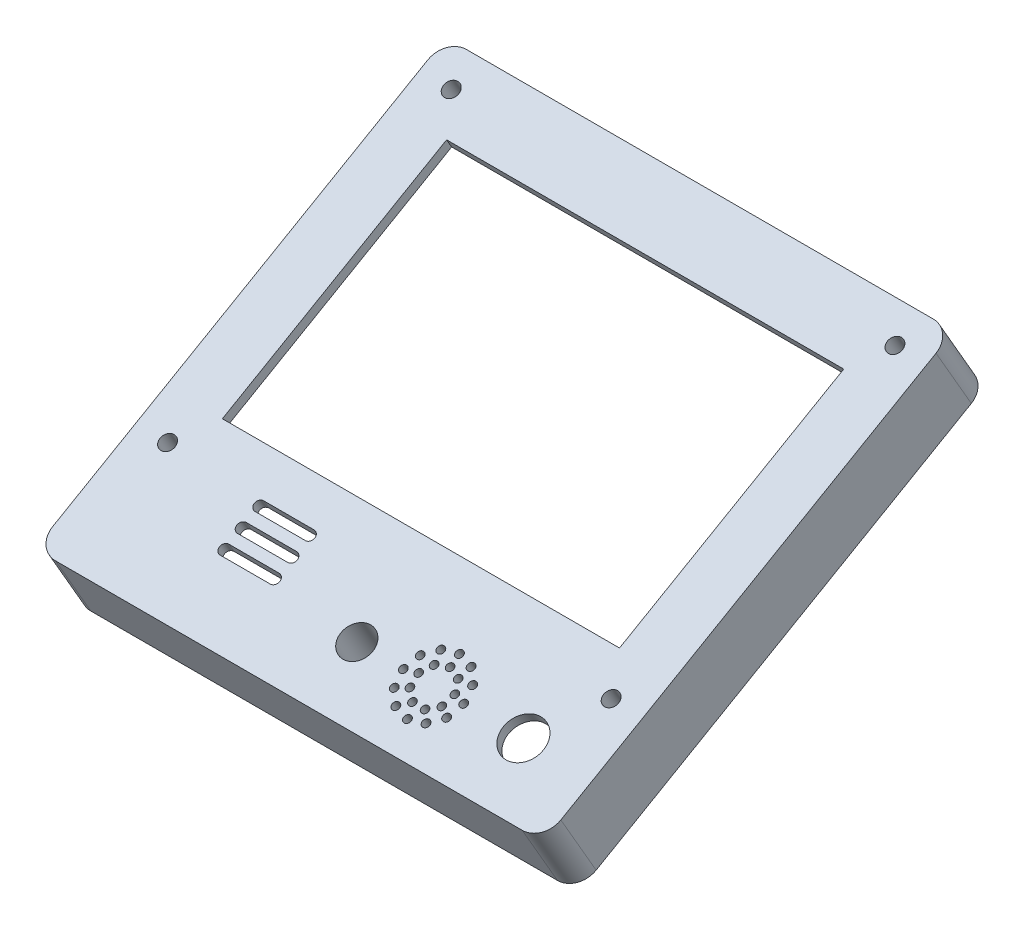
SolidWorks part; units mm, degrees
ref_plane "Front Plane" through (0, 0, 0) normal (0, 0, 1) x (1, 0, 0)
ref_plane "Top Plane" through (0, 0, 0) normal (0, 1, 0) x (1, 0, 0)
ref_plane "Right Plane" through (0, 0, 0) normal (1, 0, 0) x (0, 0, -1)
sketch "Sketch2" plane through (0, 0, 0) normal (0, 1, 0) x (1, 0, 0)
  line L0 (0, 0) -> (50081.3291, 0) construction
  line L1 (0, 0) -> (0, -110950.6715) construction
  line L2 (0, -89480) -> (38648.623, -89480) construction
  point P6 (25040.6645, 0)
  dimension "D1" = 89480
ref_plane "Plane3" through (0, 38745.9766, 22370) normal (0, 0.866, 0.5) x (1, 0, 0)
sketch "Sketch3" plane through (0, 38745.9766, 22370) normal (0, 0.866, 0.5) x (1, 0, 0)
  line L4 (-50374.8432, -6320.5279) -> (50376.1874, -6320.5279)
  line L5 (50376.1874, -6320.5279) -> (50376.1874, -100416.3212)
  line L6 (50376.1874, -100416.3212) -> (-50374.8432, -100416.3212)
  line L7 (-50374.8432, -100416.3212) -> (-50374.8432, -6320.5279)
  dimension "D1" = 100751.0306
  dimension "D2" = 94095.7933
sketch "Sketch4" plane through (0, 0, 0) normal (1, 0, 0) x (0, 0, -1)
  line L0 (0, 0) -> (-89485.0672, 0) construction
  line L1 (0, 0) -> (-110950.6715, 0) construction
  line L2 (-89485.0672, 0) -> (-89485.0672, -20894.7406) construction
extrude "Boss-Extrude1" add sketch "Sketch3" along normal blind 14000
shell "Shell1" thickness 2000
sketch "Sketch5" plane through (0, 50870.3322, 29370) normal (0, 0.866, 0.5) x (1, 0, 0)
  line L0 (-24605.495, -77761.1574) -> (-14621.2598, -77761.1574)
  line L1 (-39129.4107, -70448.8565) -> (39606.8675, -70448.8565)
  line L2 (-39129.4107, -70448.8565) -> (-39129.4107, -19112.8031)
  line L3 (-39129.4107, -19112.8031) -> (39606.8675, -19112.8031)
  line L4 (39606.8675, -70448.8565) -> (39606.8675, -19112.8031)
  line L5 (-24605.495, -79737.168) -> (-14621.2598, -79737.168)
  line L6 (-24597.3605, -81751.7796) -> (-14620.8656, -81751.7796)
  line L7 (-24597.3605, -83766.3728) -> (-14620.8656, -83766.3728)
  line L8 (-24586.8841, -85741.4185) -> (-14643.555, -85741.4185)
  line L9 (-24586.8841, -87752.0657) -> (-14643.555, -87752.0657)
  line L10 (50376.1874, -6320.5279) -> (-50374.8432, -6320.5279) construction
  line L11 (-50374.8432, -6320.5279) -> (-50374.8432, -100416.3212) construction
  line L14 (-50374.8432, -100416.3212) -> (50376.1874, -100416.3212) construction
  line L15 (50376.1874, -100416.3212) -> (50376.1874, -6320.5279) construction
  circle A0 centre (-43988.643, -12447.8612) radius 1501.7923
  circle A1 centre (43969.8589, -12425.4966) radius 1493.6873
  circle A2 centre (43990.1719, -77427.1184) radius 1490.7249
  circle A3 centre (36420.679, -88766.8916) radius 3982.1728
  circle A4 centre (3383.4287, -88760.7991) radius 3170.6094
  circle A5 centre (-43960.9906, -77415.5626) radius 1490.364
  arc A6 (-24605.495, -77761.1574) -> (-24605.495, -79737.168) centre (-24605.495, -78749.1627) ccw
  arc A7 (-24597.3605, -81751.7796) -> (-24597.3605, -83766.3728) centre (-24597.3605, -82759.0762) ccw
  arc A8 (-24586.8841, -85741.4185) -> (-24586.8841, -87752.0657) centre (-24586.8841, -86746.7421) ccw
  arc A9 (-14643.555, -87752.0657) -> (-14643.555, -85741.4185) centre (-14643.555, -86746.7421) ccw
  arc A10 (-14620.8656, -83766.3728) -> (-14620.8656, -81751.7796) centre (-14620.8656, -82759.0762) ccw
  arc A11 (-14621.2598, -79737.168) -> (-14621.2598, -77761.1574) centre (-14621.2598, -78749.1627) ccw
  circle A13 centre (12622.7096, -88782.7367) radius 737.9119
  circle A14 centre (13435.1258, -91791.6852) radius 740.8686
  circle A15 centre (15520.9408, -90608.0936) radius 724.5909
  circle A16 centre (15113.5927, -88150.56) radius 724.1259
  circle A17 centre (16340.1747, -86021.6181) radius 734.9855
  circle A18 centre (18726.3962, -88814.2471) radius 3673.2587 construction
  circle A20 centre (18752.6437, -85141.0822) radius 724.1259
  circle A21 centre (21107.5678, -86017.3111) radius 724.1259
  circle A22 centre (22348.3153, -88202.2574) radius 724.1259
  circle A23 centre (21894.3266, -90673.5605) radius 724.1259
  circle A24 centre (19958.028, -92274.8702) radius 724.1259
  circle A25 centre (17445.4352, -92256.9159) radius 724.1259
  circle A27 centre (16385.438, -85983.568) radius 724.1259 [skipped]
  circle A28 centre (15532.2183, -90628.0986) radius 724.1259 [skipped]
  circle A29 centre (18599.5006, -88783.1535) radius 5976.7909 construction
  circle A31 centre (13411.8483, -85818.0355) radius 740.8686
  circle A32 centre (15589.8357, -83623.0077) radius 740.8686
  circle A33 centre (18573.5419, -82811.0517) radius 740.8686
  circle A34 centre (21563.4854, -83599.7302) radius 740.8686
  circle A35 centre (23758.5132, -85777.7176) radius 740.8686
  circle A36 centre (24570.4692, -88761.4239) radius 740.8686
  circle A37 centre (23781.7907, -91751.3674) radius 740.8686
  circle A38 centre (21603.8033, -93946.3951) radius 740.8686
  circle A39 centre (18620.097, -94758.3512) radius 740.8686
  circle A40 centre (15630.1535, -93969.6726) radius 740.8686
  circle A41 centre (12623.1697, -88807.9789) radius 740.8686 [skipped]
  point P60 (18726.3962, -88814.2471)
  point P86 (18596.8195, -88784.7014)
  dimension "D21" = 7964.3457
  dimension "D22" = 87958.5019
  dimension "D3" = 6127.3332
  dimension "D4" = 87958.5019
  dimension "D5" = 65001.6217
  dimension "D6" = 6386.2002
  dimension "D7" = 11649.4296
  dimension "D8" = 13955.5084
  dimension "D9" = 11655.5222
  dimension "D10" = 46992.7587
  dimension "D11" = 4009.9135
  dimension "D12" = 3987.6659
  dimension "D13" = 2014.5932
  dimension "D14" = 9976.4949
  dimension "D15" = 13669.5792
  dimension "D16" = 51336.0534
  dimension "D17" = 78736.2782
  dimension "D18" = 11245.4325
  dimension "D19" = 12792.2751
  dimension "D20" = 25787.9591
  dimension "D1" = 9
  dimension "D2" = 12
sketch "Sketch6" plane through (0, 38745.9766, 22370) normal (0, -0.866, -0.5) x (1, 0, 0)
  line L0 (50376.1874, 53368.4246) -> (48347.6296, 53368.4246)
  line L1 (50376.1874, 6320.5279) -> (50376.1874, 100416.3212) construction
extrude "Cut-Extrude1" cut sketch "Sketch5" against normal through all
sketch "Sketch7" plane through (0, 49138.2814, 28370) normal (0, -0.866, -0.5) x (1, 0, 0)
  line L0 (-50374.8432, 6320.5279) -> (-50374.8432, 100416.3212) construction
  line L1 (50376.1874, 100416.3212) -> (50376.1874, 6320.5279) construction
  line L2 (-50374.8432, 100416.3212) -> (50376.1874, 100416.3212) construction
  line L3 (50376.1874, 6320.5279) -> (-50374.8432, 6320.5279) construction
  line L4 (43969.8589, 12425.4966) -> (-43988.643, 12447.8612) construction
  line L5 (-43988.643, 12447.8612) -> (-43960.9906, 77415.5626) construction
  circle A4 centre (43969.8589, 12425.4966) radius 3521.6824
  circle A5 centre (-43988.643, 12447.8612) radius 3521.6824
  circle A6 centre (-43960.9906, 77415.5626) radius 3500
  circle A7 centre (43990.1719, 77427.1184) radius 3521.6824
  circle A8 centre (3383.4287, 88760.7991) radius 4000
  dimension "D1" = 8000
  dimension "D2" = 7000
  dimension "D3" = 6386.2002
  dimension "D4" = 6406.3285
  dimension "D5" = 6386.0155
  dimension "D6" = 6413.8526
  dimension "D7" = 23000.7587
  dimension "D8" = 11655.5222
  dimension "D9" = 22989.2029
  dimension "D10" = 6104.9687
  dimension "D11" = 6127.3332
extrude "Boss-Extrude2" add sketch "Sketch7" along normal blind 6300
sketch "Sketch8" plane through (0, 49138.2814, 28370) normal (0, 0.866, 0.5) x (1, 0, 0)
  circle A0 centre (3383.4287, -88760.7991) radius 3170.6094
  circle A1 centre (-43960.9906, -77415.5626) radius 1490.364
  circle A2 centre (-43988.643, -12447.8612) radius 1501.7923
  circle A3 centre (43969.8589, -12425.4966) radius 1493.6873
  circle A4 centre (43990.1719, -77427.1184) radius 1490.7249
extrude "Cut-Extrude2" cut sketch "Sketch8" against normal through all
sketch "Sketch9" plane through (0, 38745.9766, 22370) normal (0, 0.866, 0.5) x (1, 0, 0)
  circle A0 centre (-46197.4506, -96238.9286) radius 4177.3926
fillet "Fillet1" radius 4100 4 edges at (-50374.8432, 41647.8904, 31343.7378) (50376.1874, 41647.8904, 31343.7378) (50376.1874, -5400.0062, 112833.0851) (-50374.8432, -5400.0062, 112833.0851)
